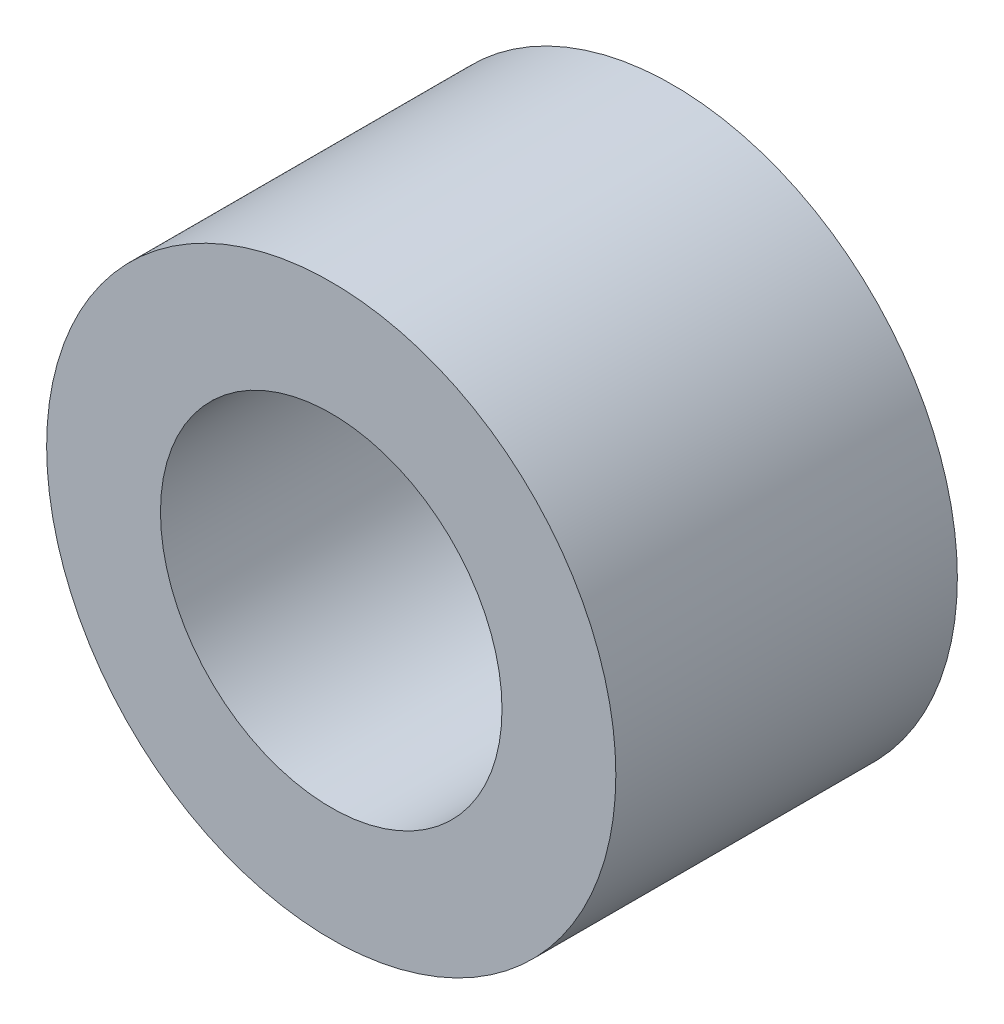
SolidWorks part; units mm, degrees
material "PTFE (general)"
ref_plane "Front Plane" through (0, 0, 0) normal (0, 0, 1) x (1, 0, 0)
ref_plane "Top Plane" through (0, 0, 0) normal (0, 1, 0) x (1, 0, 0)
ref_plane "Right Plane" through (0, 0, 0) normal (1, 0, 0) x (0, 0, -1)
sketch "Sketch1" plane through (0, 0, 0) normal (0, 0, 1) x (1, 0, 0)
  line L0 (-7.9375, 0) -> (7.9375, 0) construction
  line L1 (-4.7625, 0) -> (4.7625, 0) construction
  point P4 (0, 0)
  point P7 (0, 0)
  dimension "OD" = 15.875
  dimension "ID" = 9.525
  dimension "Wall Thickness" = 3.175
sketch "Sketch2" plane through (0, 0, 0) normal (1, 0, 0) x (0, 0, -1)
  line L0 (4.7625, 0) -> (-4.7625, 0) construction
  point P0 (19.05, 0)
  point P4 (0, 0)
  point P6 (-19.05, 0)
  dimension "D1" = 9.525
  dimension "D2" = 23.8125
  dimension "D3" = 23.8125
sketch "Sketch3" plane through (0, 0, 0) normal (0, 0, 1) x (1, 0, 0)
  circle A0 centre (0, 0) radius 7.9375
  circle A1 centre (0, 0) radius 4.7625
  dimension "D1" = 15.875
extrude "Boss-Extrude1" add sketch "Sketch3" along normal mid plane 9.525
equation "\"D2@Sketch2\"=\"OD@Sketch1\" * 1.5"
equation "\"D3@Sketch2\"=\"D2@Sketch2\""
equation "\"D1@Sketch3\" = \"OD@Sketch1\""
equation "\"D1@Boss-Extrude1\"=\"D1@Sketch2\""
